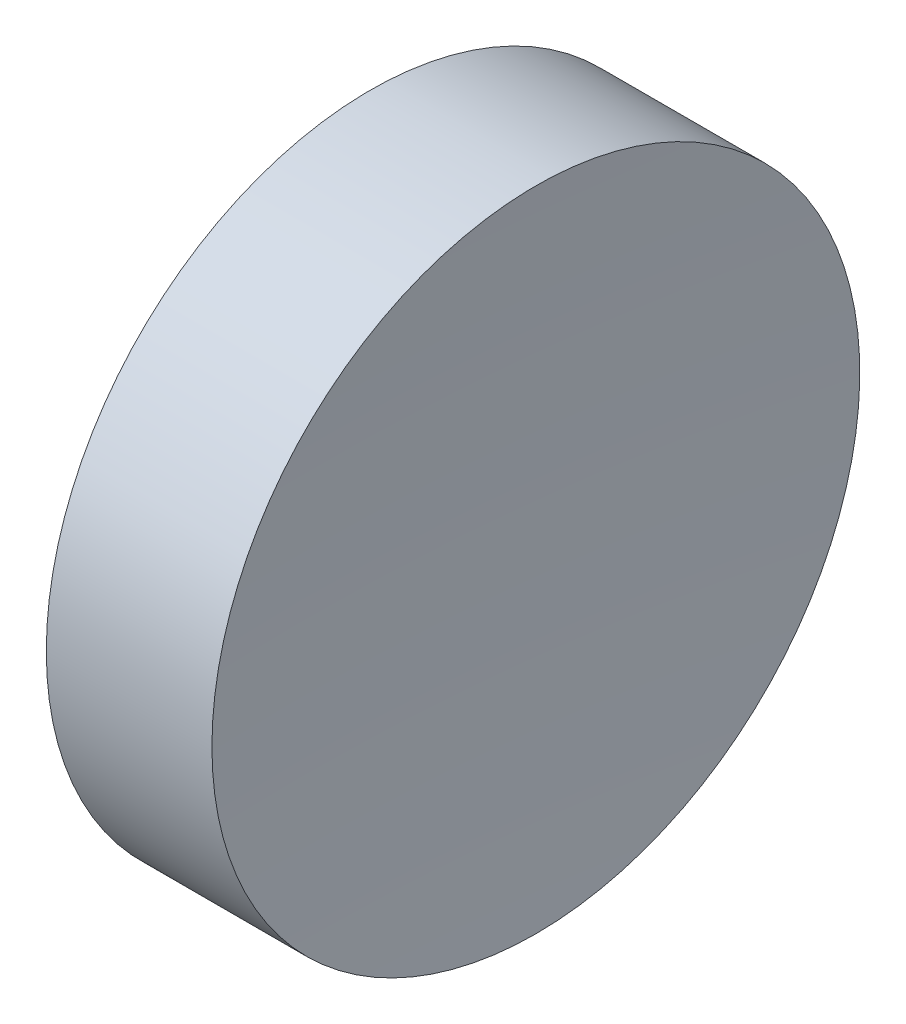
SolidWorks part; units mm, degrees
ref_plane "前视基准面" through (0, 0, 0) normal (0, 0, 1) x (1, 0, 0)
ref_plane "上视基准面" through (0, 0, 0) normal (0, 1, 0) x (1, 0, 0)
ref_plane "右视基准面" through (0, 0, 0) normal (1, 0, 0) x (0, 0, -1)
sketch "草图1" plane through (0, 0, 0) normal (0, 0, 1) x (1, 0, 0)
  line L0 (54.4926, 34.689) -> (66.3882, 34.689) construction
  line L1 (57.5463, 34.689) -> (57.5463, 40.939)
  line L2 (57.5463, 40.939) -> (60.7418, 40.939)
  line L3 (60.5463, 34.689) -> (57.5463, 34.689)
  arc A0 (60.7418, 40.939) -> (60.5463, 34.689) centre (160.5463, 34.689) ccw
  dimension "D1" = 3.1955
revolve "旋转1" add sketch "草图1" angle 360 about L0
